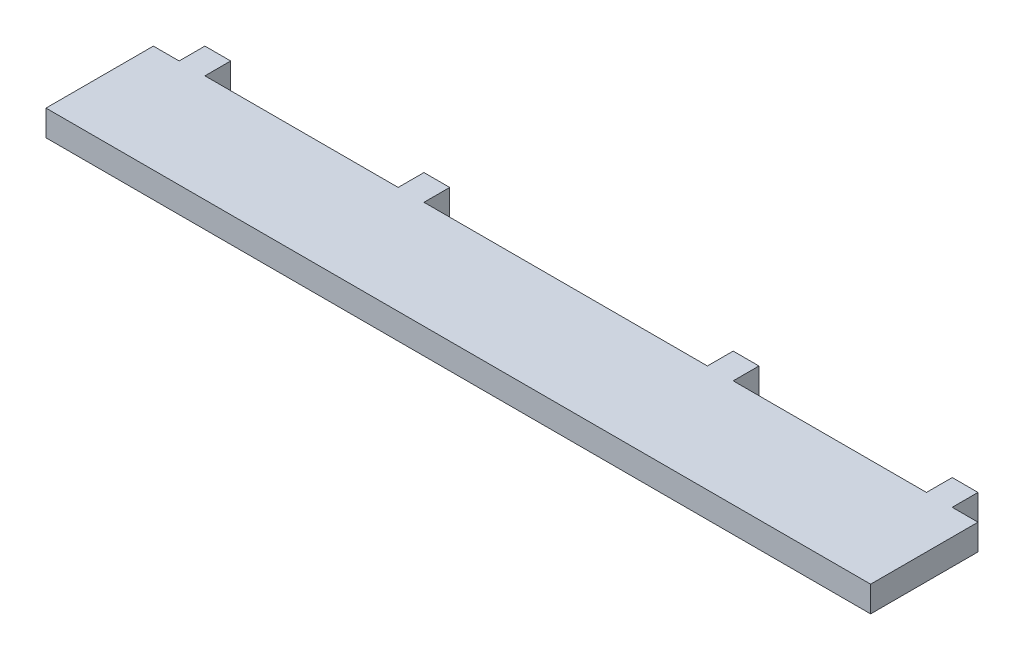
SolidWorks part; units mm, degrees
material "Pine"
ref_plane "정면" through (0, 0, 0) normal (0, 0, 1) x (1, 0, 0)
ref_plane "윗면" through (0, 0, 0) normal (0, 1, 0) x (1, 0, 0)
ref_plane "우측면" through (0, 0, 0) normal (1, 0, 0) x (0, 0, -1)
sketch "Sketch1" plane through (0, 0, 0) normal (0, 0, 1) x (1, 0, 0)
  line L0 (0, -73.9429) -> (0, 102.0491) construction
  line L1 (96, 0) -> (-96, 0)
  line L2 (-96, 0) -> (-96, 6)
  line L3 (-96, 6) -> (96, 6)
  line L4 (96, 0) -> (96, 6)
  point P8 (0, 0)
  point P9 (0, 6)
  dimension "D1" = 96
  dimension "D2" = 6
extrude "Boss-Extrude1" add sketch "Sketch1" along normal blind 25
sketch "Sketch2" plane through (0, 0, 0) normal (0, 1, 0) x (1, 0, 0)
  line L0 (0, 31.412) -> (0, -47.2051) construction
  line L1 (-90, 0) -> (-90, 6)
  line L2 (-96, 0) -> (96, 0) construction
  line L3 (-90, 6) -> (-84, 6)
  line L4 (-84, 6) -> (-84, 0)
  line L5 (-84, 0) -> (-90, 0)
  line L6 (-96, -25) -> (-96, 0) construction
  line L7 (-39, 0) -> (-39, 6)
  line L8 (-39, 6) -> (-33, 6)
  line L9 (-33, 6) -> (-33, 0)
  line L10 (-33, 0) -> (-39, 0)
  line L11 (33, 0) -> (39, 0)
  line L12 (33, 6) -> (33, 0)
  line L13 (39, 6) -> (33, 6)
  line L14 (39, 0) -> (39, 6)
  line L15 (84, 0) -> (90, 0)
  line L16 (84, 6) -> (84, 0)
  line L17 (90, 6) -> (84, 6)
  line L18 (90, 0) -> (90, 6)
  dimension "D1" = 6
  dimension "D2" = 6
  dimension "D3" = 6
  dimension "D4" = 6
  dimension "D5" = 6
  dimension "D6" = 45
extrude "Boss-Extrude3" add sketch "Sketch2" along normal blind 6
